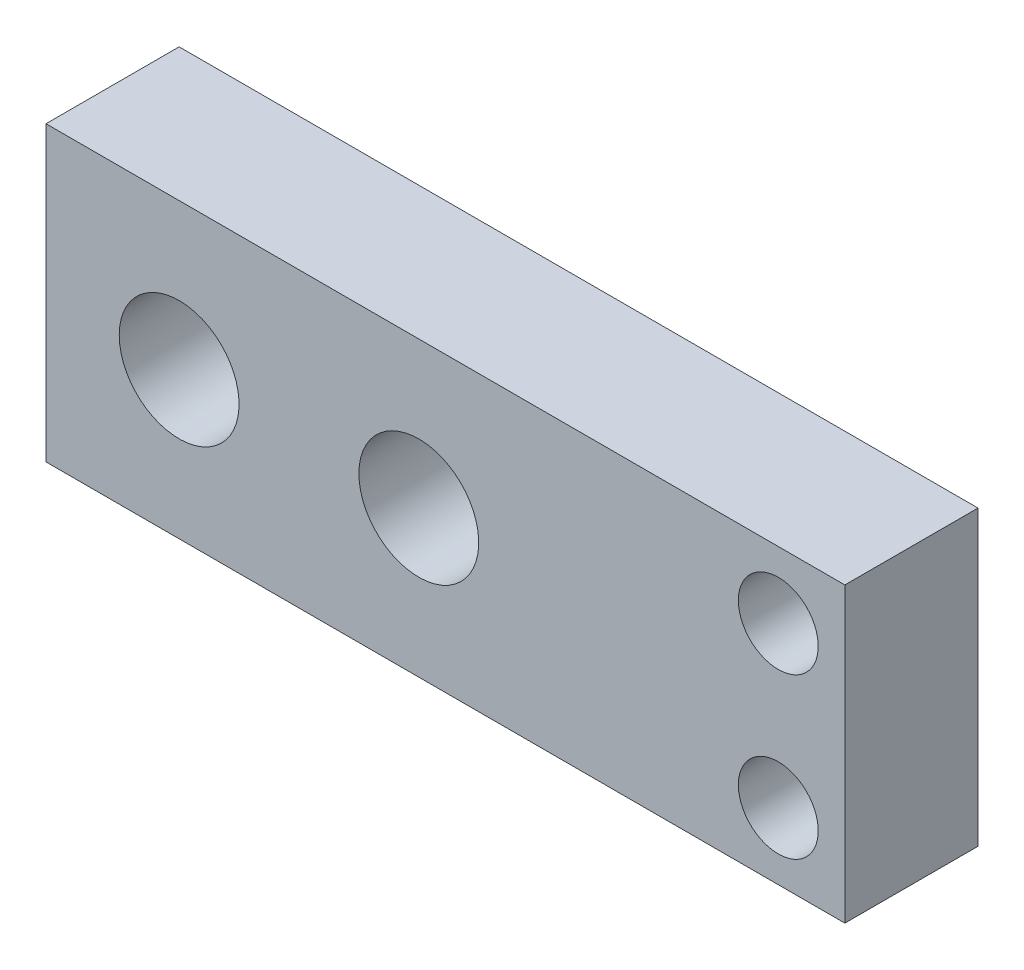
SolidWorks part; units mm, degrees
ref_plane "Front Plane" through (0, 0, 0) normal (0, 0, 1) x (1, 0, 0)
ref_plane "Top Plane" through (0, 0, 0) normal (0, 1, 0) x (1, 0, 0)
ref_plane "Right Plane" through (0, 0, 0) normal (1, 0, 0) x (0, 0, -1)
sketch "Sketch1" plane through (0, 0, 0) normal (0, 0, 1) x (1, 0, 0)
  line L1 (-30, -11) -> (30, -11)
  line L2 (-30, -11) -> (-30, 11)
  line L3 (-30, 11) -> (30, 11)
  line L4 (30, -11) -> (30, 11)
  line L5 (-30, -11) -> (30, 11) construction
  line L6 (-30, 11) -> (30, -11) construction
  point P0 (0, 0)
  dimension "D1" = 60
  dimension "D2" = 22
extrude "Boss-Extrude1" add sketch "Sketch1" along normal blind 10
sketch "Sketch2" plane through (0, 0, 10) normal (0, 0, 1) x (1, 0, 0)
  line L1 (20, -11) -> (30, -11)
  line L2 (20, -11) -> (20, 11)
  line L3 (20, 11) -> (30, 11)
  line L4 (30, -11) -> (30, 11)
  line L5 (20, -11) -> (30, 11) construction
  line L6 (20, 11) -> (30, -11) construction
  point P0 (25, 0)
  dimension "D1" = 10
sketch "Sketch3" plane through (0, 0, 0) normal (0, 0, -1) x (-1, 0, 0)
  line L0 (30, 11) -> (30, -11) construction
  circle A0 centre (20, 0) radius 4.5
  circle A1 centre (2, 0) radius 4.5
  point P4 (30, 0)
  dimension "D2" = 18
  dimension "D3" = 9
  dimension "D4" = 9
  dimension "D1" = 10
extrude "Cut-Extrude1" cut sketch "Sketch3" against normal blind 60
sketch "Sketch4" plane through (0, 0, 0) normal (0, 0, -1) x (-1, 0, 0)
  line L0 (-20, 11) -> (-30, 11) construction
  line L1 (-20, -11) -> (-30, -11) construction
  line L2 (-30, -11) -> (-30, 11) construction
  circle A0 centre (-25, 6) radius 3
  circle A1 centre (-25, -6) radius 3
  dimension "D1" = 6
  dimension "D2" = 6
  dimension "D3" = 5
  dimension "D4" = 5
  dimension "D5" = 5
  dimension "D6" = 5
extrude "Cut-Extrude2" cut sketch "Sketch4" against normal blind 60
